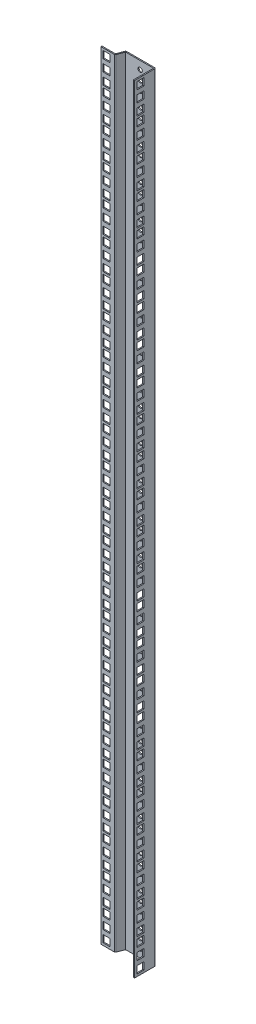
SolidWorks part; units mm, degrees
material "AISI 1020 钢，冷轧"
ref_plane "前视基准面" through (0, 0, 0) normal (0, 0, 1) x (1, 0, 0)
ref_plane "上视基准面" through (0, 0, 0) normal (0, 1, 0) x (1, 0, 0)
ref_plane "右视基准面" through (0, 0, 0) normal (1, 0, 0) x (0, 0, -1)
sketch "草图1" plane through (0, 0, 0) normal (0, 1, 0) x (1, 0, 0)
  line L0 (-1.5473, -0.7176) -> (16.9527, -0.7176)
  line L2 (16.9527, 0.7824) -> (-1.5473, 0.7824)
  line L3 (-1.5473, 0.7824) -> (-1.5473, -0.7176)
  line L4 (21.9526, 9.7824) -> (18.356, 0.2527)
  line L6 (21.9526, 11.2824) -> (60.4526, 11.2824)
  line L8 (60.4526, 9.7824) -> (21.9526, 9.7824)
  line L9 (16.9527, 0.7824) -> (20.5492, 10.312)
  line L11 (61.9526, 9.7824) -> (61.9526, -17.7176)
  line L12 (60.4526, 9.7824) -> (60.4526, -17.7176)
  line L13 (60.4526, -17.7176) -> (61.9526, -17.7176)
  arc A0 (21.9526, 11.2824) -> (20.5492, 10.312) centre (21.9526, 9.7824) ccw
  arc A1 (18.356, 0.2527) -> (16.9527, -0.7176) centre (16.9527, 0.7824) cw
  arc A2 (60.4526, 11.2824) -> (61.9526, 9.7824) centre (60.4526, 9.7824) cw
extrude "凸台-拉伸1" add sketch "草图1" along normal blind 1070
sketch "草图2" plane through (0, 0, -9.7824) normal (0, 0, 1) x (1, 0, 0)
  line L0 (1.4527, 666.95) -> (1.4527, 657.0516)
  line L1 (1.4527, 1067) -> (1.4527, 1057.1016)
  line L3 (1.4527, 1022.55) -> (1.4527, 1012.6516)
  line L4 (1.4527, 622.5) -> (1.4527, 612.6016)
  line L5 (1.4527, 1067) -> (11.0527, 1067)
  line L6 (11.0527, 1067) -> (11.0527, 1057.1016)
  line L7 (11.0527, 1057.1016) -> (1.4527, 1057.1016)
  line L8 (1.4527, 1035.4484) -> (1.4527, 1025.55)
  line L9 (1.4527, 1035.4484) -> (11.0527, 1035.4484)
  line L10 (11.0527, 1035.4484) -> (11.0527, 1025.55)
  line L11 (11.0527, 1025.55) -> (1.4527, 1025.55)
  line L12 (1.4527, 1022.55) -> (11.0527, 1022.55)
  line L13 (11.0527, 1022.55) -> (11.0527, 1012.6516)
  line L14 (1.4527, 1051.2242) -> (1.4527, 1041.3258)
  line L15 (1.4527, 1051.2242) -> (11.0527, 1051.2242)
  line L16 (11.0527, 1051.2242) -> (11.0527, 1041.3258)
  line L17 (11.0527, 1041.3258) -> (1.4527, 1041.3258)
  line L18 (1.4527, 889.2) -> (1.4527, 879.3016)
  line L19 (11.0527, 1012.6516) -> (1.4527, 1012.6516)
  line L20 (1.4527, 990.9984) -> (1.4527, 981.1)
  line L21 (1.4527, 990.9984) -> (11.0527, 990.9984)
  line L22 (11.0527, 990.9984) -> (11.0527, 981.1)
  line L23 (11.0527, 981.1) -> (1.4527, 981.1)
  line L24 (1.4527, 1006.7742) -> (1.4527, 996.8758)
  line L25 (1.4527, 1006.7742) -> (11.0527, 1006.7742)
  line L26 (11.0527, 1006.7742) -> (11.0527, 996.8758)
  line L27 (11.0527, 996.8758) -> (1.4527, 996.8758)
  line L28 (1.4527, 666.95) -> (11.0527, 666.95)
  line L29 (1.4527, 978.1) -> (1.4527, 968.2016)
  line L30 (1.4527, 933.65) -> (1.4527, 923.7516)
  line L31 (1.4527, 978.1) -> (11.0527, 978.1)
  line L32 (11.0527, 978.1) -> (11.0527, 968.2016)
  line L33 (11.0527, 968.2016) -> (1.4527, 968.2016)
  line L34 (1.4527, 946.5484) -> (1.4527, 936.65)
  line L35 (1.4527, 946.5484) -> (11.0527, 946.5484)
  line L36 (11.0527, 946.5484) -> (11.0527, 936.65)
  line L37 (11.0527, 936.65) -> (1.4527, 936.65)
  line L38 (1.4527, 933.65) -> (11.0527, 933.65)
  line L39 (11.0527, 933.65) -> (11.0527, 923.7516)
  line L40 (1.4527, 962.3242) -> (1.4527, 952.4258)
  line L41 (1.4527, 962.3242) -> (11.0527, 962.3242)
  line L42 (11.0527, 962.3242) -> (11.0527, 952.4258)
  line L43 (11.0527, 952.4258) -> (1.4527, 952.4258)
  line L44 (11.0527, 923.7516) -> (1.4527, 923.7516)
  line L45 (1.4527, 902.0984) -> (1.4527, 892.2)
  line L46 (1.4527, 902.0984) -> (11.0527, 902.0984)
  line L47 (11.0527, 902.0984) -> (11.0527, 892.2)
  line L48 (11.0527, 892.2) -> (1.4527, 892.2)
  line L49 (1.4527, 917.8742) -> (1.4527, 907.9758)
  line L50 (1.4527, 917.8742) -> (11.0527, 917.8742)
  line L51 (11.0527, 917.8742) -> (11.0527, 907.9758)
  line L52 (11.0527, 907.9758) -> (1.4527, 907.9758)
  line L53 (1.4527, 844.75) -> (1.4527, 834.8516)
  line L54 (1.4527, 889.2) -> (11.0527, 889.2)
  line L55 (11.0527, 889.2) -> (11.0527, 879.3016)
  line L56 (11.0527, 879.3016) -> (1.4527, 879.3016)
  line L57 (1.4527, 857.6484) -> (1.4527, 847.75)
  line L58 (1.4527, 857.6484) -> (11.0527, 857.6484)
  line L59 (11.0527, 857.6484) -> (11.0527, 847.75)
  line L60 (11.0527, 847.75) -> (1.4527, 847.75)
  line L61 (1.4527, 844.75) -> (11.0527, 844.75)
  line L62 (11.0527, 844.75) -> (11.0527, 834.8516)
  line L63 (1.4527, 873.4242) -> (1.4527, 863.5258)
  line L64 (1.4527, 873.4242) -> (11.0527, 873.4242)
  line L65 (11.0527, 873.4242) -> (11.0527, 863.5258)
  line L66 (11.0527, 863.5258) -> (1.4527, 863.5258)
  line L67 (11.0527, 834.8516) -> (1.4527, 834.8516)
  line L68 (1.4527, 813.1984) -> (1.4527, 803.3)
  line L69 (1.4527, 813.1984) -> (11.0527, 813.1984)
  line L70 (11.0527, 813.1984) -> (11.0527, 803.3)
  line L71 (11.0527, 803.3) -> (1.4527, 803.3)
  line L72 (1.4527, 828.9742) -> (1.4527, 819.0758)
  line L73 (1.4527, 828.9742) -> (11.0527, 828.9742)
  line L74 (11.0527, 828.9742) -> (11.0527, 819.0758)
  line L75 (11.0527, 819.0758) -> (1.4527, 819.0758)
  line L76 (33.9626, 832.025) -> (33.9626, 816.025)
  line L77 (49.9426, 816.025) -> (49.9426, 832.025)
  line L91 (1.4527, 800.3) -> (1.4527, 790.4016)
  line L92 (1.4527, 800.3) -> (11.0527, 800.3)
  line L93 (11.0527, 800.3) -> (11.0527, 790.4016)
  line L94 (11.0527, 790.4016) -> (1.4527, 790.4016)
  line L95 (1.4527, 768.7484) -> (1.4527, 758.85)
  line L96 (1.4527, 768.7484) -> (11.0527, 768.7484)
  line L97 (11.0527, 768.7484) -> (11.0527, 758.85)
  line L98 (11.0527, 758.85) -> (1.4527, 758.85)
  line L99 (1.4527, 784.5242) -> (1.4527, 774.6258)
  line L100 (1.4527, 784.5242) -> (11.0527, 784.5242)
  line L101 (11.0527, 784.5242) -> (11.0527, 774.6258)
  line L102 (11.0527, 774.6258) -> (1.4527, 774.6258)
  line L103 (33.9626, 787.575) -> (33.9626, 771.575)
  line L104 (49.9426, 771.575) -> (49.9426, 787.575)
  line L106 (1.4527, 755.85) -> (1.4527, 745.9516)
  line L107 (1.4527, 755.85) -> (11.0527, 755.85)
  line L108 (11.0527, 755.85) -> (11.0527, 745.9516)
  line L109 (11.0527, 745.9516) -> (1.4527, 745.9516)
  line L110 (1.4527, 724.2984) -> (1.4527, 714.4)
  line L111 (1.4527, 724.2984) -> (11.0527, 724.2984)
  line L112 (11.0527, 724.2984) -> (11.0527, 714.4)
  line L113 (11.0527, 714.4) -> (1.4527, 714.4)
  line L114 (1.4527, 740.0742) -> (1.4527, 730.1758)
  line L115 (1.4527, 740.0742) -> (11.0527, 740.0742)
  line L116 (11.0527, 740.0742) -> (11.0527, 730.1758)
  line L117 (11.0527, 730.1758) -> (1.4527, 730.1758)
  line L118 (33.9626, 743.125) -> (33.9626, 727.125)
  line L119 (49.9426, 727.125) -> (49.9426, 743.125)
  line L120 (1.4527, 711.4) -> (1.4527, 701.5016)
  line L121 (1.4527, 711.4) -> (11.0527, 711.4)
  line L122 (11.0527, 711.4) -> (11.0527, 701.5016)
  line L123 (11.0527, 701.5016) -> (1.4527, 701.5016)
  line L124 (1.4527, 679.8484) -> (1.4527, 669.95)
  line L125 (1.4527, 679.8484) -> (11.0527, 679.8484)
  line L126 (11.0527, 679.8484) -> (11.0527, 669.95)
  line L127 (11.0527, 669.95) -> (1.4527, 669.95)
  line L128 (1.4527, 695.6242) -> (1.4527, 685.7258)
  line L129 (1.4527, 695.6242) -> (11.0527, 695.6242)
  line L130 (11.0527, 695.6242) -> (11.0527, 685.7258)
  line L131 (11.0527, 685.7258) -> (1.4527, 685.7258)
  line L132 (33.9626, 698.675) -> (33.9626, 682.675)
  line L133 (49.9426, 682.675) -> (49.9426, 698.675)
  line L134 (11.0527, 666.95) -> (11.0527, 657.0516)
  line L135 (11.0527, 657.0516) -> (1.4527, 657.0516)
  line L136 (1.4527, 635.3984) -> (1.4527, 625.5)
  line L137 (1.4527, 635.3984) -> (11.0527, 635.3984)
  line L138 (11.0527, 635.3984) -> (11.0527, 625.5)
  line L139 (11.0527, 625.5) -> (1.4527, 625.5)
  line L140 (1.4527, 622.5) -> (11.0527, 622.5)
  line L141 (11.0527, 622.5) -> (11.0527, 612.6016)
  line L142 (1.4527, 651.1742) -> (1.4527, 641.2758)
  line L143 (1.4527, 651.1742) -> (11.0527, 651.1742)
  line L144 (11.0527, 651.1742) -> (11.0527, 641.2758)
  line L145 (11.0527, 641.2758) -> (1.4527, 641.2758)
  line L146 (1.4527, 489.15) -> (1.4527, 479.2516)
  line L147 (11.0527, 612.6016) -> (1.4527, 612.6016)
  line L148 (1.4527, 590.9484) -> (1.4527, 581.05)
  line L149 (1.4527, 590.9484) -> (11.0527, 590.9484)
  line L150 (11.0527, 590.9484) -> (11.0527, 581.05)
  line L151 (11.0527, 581.05) -> (1.4527, 581.05)
  line L152 (1.4527, 606.7242) -> (1.4527, 596.8258)
  line L153 (1.4527, 606.7242) -> (11.0527, 606.7242)
  line L154 (11.0527, 606.7242) -> (11.0527, 596.8258)
  line L155 (11.0527, 596.8258) -> (1.4527, 596.8258)
  line L156 (1.4527, 578.05) -> (1.4527, 568.1516)
  line L157 (1.4527, 533.6) -> (1.4527, 523.7016)
  line L158 (1.4527, 578.05) -> (11.0527, 578.05)
  line L159 (11.0527, 578.05) -> (11.0527, 568.1516)
  line L160 (11.0527, 568.1516) -> (1.4527, 568.1516)
  line L161 (1.4527, 546.4984) -> (1.4527, 536.6)
  line L162 (1.4527, 546.4984) -> (11.0527, 546.4984)
  line L163 (11.0527, 546.4984) -> (11.0527, 536.6)
  line L164 (11.0527, 536.6) -> (1.4527, 536.6)
  line L165 (1.4527, 533.6) -> (11.0527, 533.6)
  line L166 (11.0527, 533.6) -> (11.0527, 523.7016)
  line L167 (1.4527, 562.2742) -> (1.4527, 552.3758)
  line L168 (1.4527, 562.2742) -> (11.0527, 562.2742)
  line L169 (11.0527, 562.2742) -> (11.0527, 552.3758)
  line L170 (11.0527, 552.3758) -> (1.4527, 552.3758)
  line L171 (11.0527, 523.7016) -> (1.4527, 523.7016)
  line L172 (1.4527, 502.0484) -> (1.4527, 492.15)
  line L173 (1.4527, 502.0484) -> (11.0527, 502.0484)
  line L174 (11.0527, 502.0484) -> (11.0527, 492.15)
  line L175 (11.0527, 492.15) -> (1.4527, 492.15)
  line L176 (1.4527, 517.8242) -> (1.4527, 507.9258)
  line L177 (1.4527, 517.8242) -> (11.0527, 517.8242)
  line L178 (11.0527, 517.8242) -> (11.0527, 507.9258)
  line L179 (11.0527, 507.9258) -> (1.4527, 507.9258)
  line L180 (1.4527, 444.7) -> (1.4527, 434.8016)
  line L181 (1.4527, 489.15) -> (11.0527, 489.15)
  line L182 (11.0527, 489.15) -> (11.0527, 479.2516)
  line L183 (11.0527, 479.2516) -> (1.4527, 479.2516)
  line L184 (1.4527, 457.5984) -> (1.4527, 447.7)
  line L185 (1.4527, 457.5984) -> (11.0527, 457.5984)
  line L186 (11.0527, 457.5984) -> (11.0527, 447.7)
  line L187 (11.0527, 447.7) -> (1.4527, 447.7)
  line L188 (1.4527, 444.7) -> (11.0527, 444.7)
  line L189 (11.0527, 444.7) -> (11.0527, 434.8016)
  line L190 (1.4527, 473.3742) -> (1.4527, 463.4758)
  line L191 (1.4527, 473.3742) -> (11.0527, 473.3742)
  line L192 (11.0527, 473.3742) -> (11.0527, 463.4758)
  line L193 (11.0527, 463.4758) -> (1.4527, 463.4758)
  line L194 (11.0527, 434.8016) -> (1.4527, 434.8016)
  line L195 (1.4527, 413.1484) -> (1.4527, 403.25)
  line L196 (1.4527, 413.1484) -> (11.0527, 413.1484)
  line L197 (11.0527, 413.1484) -> (11.0527, 403.25)
  line L198 (11.0527, 403.25) -> (1.4527, 403.25)
  line L199 (1.4527, 428.9242) -> (1.4527, 419.0258)
  line L200 (1.4527, 428.9242) -> (11.0527, 428.9242)
  line L201 (11.0527, 428.9242) -> (11.0527, 419.0258)
  line L202 (11.0527, 419.0258) -> (1.4527, 419.0258)
  line L203 (33.9626, 431.975) -> (33.9626, 415.975)
  line L204 (49.9426, 415.975) -> (49.9426, 431.975)
  line L205 (1.4527, 400.25) -> (1.4527, 390.3516)
  line L206 (1.4527, 400.25) -> (11.0527, 400.25)
  line L207 (11.0527, 400.25) -> (11.0527, 390.3516)
  line L208 (11.0527, 390.3516) -> (1.4527, 390.3516)
  line L209 (1.4527, 368.6984) -> (1.4527, 358.8)
  line L210 (1.4527, 368.6984) -> (11.0527, 368.6984)
  line L211 (11.0527, 368.6984) -> (11.0527, 358.8)
  line L212 (11.0527, 358.8) -> (1.4527, 358.8)
  line L213 (1.4527, 384.4742) -> (1.4527, 374.5758)
  line L214 (1.4527, 384.4742) -> (11.0527, 384.4742)
  line L215 (11.0527, 384.4742) -> (11.0527, 374.5758)
  line L216 (11.0527, 374.5758) -> (1.4527, 374.5758)
  line L217 (33.9626, 387.525) -> (33.9626, 371.525)
  line L218 (49.9426, 371.525) -> (49.9426, 387.525)
  line L220 (1.4527, 355.8) -> (1.4527, 345.9016)
  line L221 (1.4527, 355.8) -> (11.0527, 355.8)
  line L222 (11.0527, 355.8) -> (11.0527, 345.9016)
  line L223 (11.0527, 345.9016) -> (1.4527, 345.9016)
  line L224 (1.4527, 324.2484) -> (1.4527, 314.35)
  line L225 (1.4527, 324.2484) -> (11.0527, 324.2484)
  line L226 (11.0527, 324.2484) -> (11.0527, 314.35)
  line L227 (11.0527, 314.35) -> (1.4527, 314.35)
  line L228 (1.4527, 340.0242) -> (1.4527, 330.1258)
  line L229 (1.4527, 340.0242) -> (11.0527, 340.0242)
  line L230 (11.0527, 340.0242) -> (11.0527, 330.1258)
  line L231 (11.0527, 330.1258) -> (1.4527, 330.1258)
  line L232 (33.9626, 343.075) -> (33.9626, 327.075)
  line L233 (49.9426, 327.075) -> (49.9426, 343.075)
  line L234 (1.4527, 311.35) -> (1.4527, 301.4516)
  line L235 (1.4527, 311.35) -> (11.0527, 311.35)
  line L236 (11.0527, 311.35) -> (11.0527, 301.4516)
  line L237 (11.0527, 301.4516) -> (1.4527, 301.4516)
  line L238 (1.4527, 279.7984) -> (1.4527, 269.9)
  line L239 (1.4527, 279.7984) -> (11.0527, 279.7984)
  line L240 (11.0527, 279.7984) -> (11.0527, 269.9)
  line L241 (11.0527, 269.9) -> (1.4527, 269.9)
  line L242 (1.4527, 295.5742) -> (1.4527, 285.6758)
  line L243 (1.4527, 295.5742) -> (11.0527, 295.5742)
  line L244 (11.0527, 295.5742) -> (11.0527, 285.6758)
  line L245 (11.0527, 285.6758) -> (1.4527, 285.6758)
  line L246 (33.9626, 298.625) -> (33.9626, 282.625)
  line L247 (49.9426, 282.625) -> (49.9426, 298.625)
  line L248 (1.4527, 266.9) -> (1.4527, 257.0016)
  line L249 (1.4527, 222.45) -> (1.4527, 212.5516)
  line L250 (1.4527, 266.9) -> (11.0527, 266.9)
  line L251 (11.0527, 266.9) -> (11.0527, 257.0016)
  line L252 (11.0527, 257.0016) -> (1.4527, 257.0016)
  line L253 (1.4527, 235.3484) -> (1.4527, 225.45)
  line L254 (1.4527, 235.3484) -> (11.0527, 235.3484)
  line L255 (11.0527, 235.3484) -> (11.0527, 225.45)
  line L256 (11.0527, 225.45) -> (1.4527, 225.45)
  line L257 (1.4527, 222.45) -> (11.0527, 222.45)
  line L258 (11.0527, 222.45) -> (11.0527, 212.5516)
  line L259 (1.4527, 251.1242) -> (1.4527, 241.2258)
  line L260 (1.4527, 251.1242) -> (11.0527, 251.1242)
  line L261 (11.0527, 251.1242) -> (11.0527, 241.2258)
  line L262 (11.0527, 241.2258) -> (1.4527, 241.2258)
  line L263 (1.4527, 89.1) -> (1.4527, 79.2016)
  line L264 (11.0527, 212.5516) -> (1.4527, 212.5516)
  line L265 (1.4527, 190.8984) -> (1.4527, 181)
  line L266 (1.4527, 190.8984) -> (11.0527, 190.8984)
  line L267 (11.0527, 190.8984) -> (11.0527, 181)
  line L268 (11.0527, 181) -> (1.4527, 181)
  line L269 (1.4527, 206.6742) -> (1.4527, 196.7758)
  line L270 (1.4527, 206.6742) -> (11.0527, 206.6742)
  line L271 (11.0527, 206.6742) -> (11.0527, 196.7758)
  line L272 (11.0527, 196.7758) -> (1.4527, 196.7758)
  line L273 (1.4527, 178) -> (1.4527, 168.1016)
  line L274 (1.4527, 133.55) -> (1.4527, 123.6516)
  line L275 (1.4527, 178) -> (11.0527, 178)
  line L276 (11.0527, 178) -> (11.0527, 168.1016)
  line L277 (11.0527, 168.1016) -> (1.4527, 168.1016)
  line L278 (1.4527, 146.4484) -> (1.4527, 136.55)
  line L279 (1.4527, 146.4484) -> (11.0527, 146.4484)
  line L280 (11.0527, 146.4484) -> (11.0527, 136.55)
  line L281 (11.0527, 136.55) -> (1.4527, 136.55)
  line L282 (1.4527, 133.55) -> (11.0527, 133.55)
  line L283 (11.0527, 133.55) -> (11.0527, 123.6516)
  line L284 (1.4527, 162.2242) -> (1.4527, 152.3258)
  line L285 (1.4527, 162.2242) -> (11.0527, 162.2242)
  line L286 (11.0527, 162.2242) -> (11.0527, 152.3258)
  line L287 (11.0527, 152.3258) -> (1.4527, 152.3258)
  line L288 (11.0527, 123.6516) -> (1.4527, 123.6516)
  line L289 (1.4527, 101.9984) -> (1.4527, 92.1)
  line L290 (1.4527, 101.9984) -> (11.0527, 101.9984)
  line L291 (11.0527, 101.9984) -> (11.0527, 92.1)
  line L292 (11.0527, 92.1) -> (1.4527, 92.1)
  line L293 (1.4527, 117.7742) -> (1.4527, 107.8758)
  line L294 (1.4527, 117.7742) -> (11.0527, 117.7742)
  line L295 (11.0527, 117.7742) -> (11.0527, 107.8758)
  line L296 (11.0527, 107.8758) -> (1.4527, 107.8758)
  line L297 (1.4527, 44.65) -> (1.4527, 34.7516)
  line L298 (1.4527, 89.1) -> (11.0527, 89.1)
  line L299 (11.0527, 89.1) -> (11.0527, 79.2016)
  line L300 (11.0527, 79.2016) -> (1.4527, 79.2016)
  line L301 (1.4527, 57.5484) -> (1.4527, 47.65)
  line L302 (1.4527, 57.5484) -> (11.0527, 57.5484)
  line L303 (11.0527, 57.5484) -> (11.0527, 47.65)
  line L304 (11.0527, 47.65) -> (1.4527, 47.65)
  line L305 (1.4527, 44.65) -> (11.0527, 44.65)
  line L306 (11.0527, 44.65) -> (11.0527, 34.7516)
  line L307 (1.4527, 73.3242) -> (1.4527, 63.4258)
  line L308 (1.4527, 73.3242) -> (11.0527, 73.3242)
  line L309 (11.0527, 73.3242) -> (11.0527, 63.4258)
  line L310 (11.0527, 63.4258) -> (1.4527, 63.4258)
  line L311 (11.0527, 34.7516) -> (1.4527, 34.7516)
  line L312 (1.4527, 13.0984) -> (1.4527, 3.2)
  line L313 (1.4527, 13.0984) -> (11.0527, 13.0984)
  line L314 (11.0527, 13.0984) -> (11.0527, 3.2)
  line L315 (11.0527, 3.2) -> (1.4527, 3.2)
  line L316 (1.4527, 28.8742) -> (1.4527, 18.9758)
  line L317 (1.4527, 28.8742) -> (11.0527, 28.8742)
  line L318 (11.0527, 28.8742) -> (11.0527, 18.9758)
  line L319 (11.0527, 18.9758) -> (1.4527, 18.9758)
  circle A0 centre (41.9526, 1046.275) radius 3
  circle A1 centre (41.9526, 1058.775) radius 3
  circle A2 centre (41.9526, 1033.775) radius 3
  circle A3 centre (41.9526, 1001.825) radius 3
  circle A4 centre (41.9526, 1014.325) radius 3
  circle A5 centre (41.9526, 989.325) radius 3
  circle A6 centre (41.9526, 957.375) radius 3
  circle A7 centre (41.9526, 969.875) radius 3
  circle A8 centre (41.9526, 944.875) radius 3
  circle A9 centre (41.9526, 912.925) radius 3
  circle A10 centre (41.9526, 925.425) radius 3
  circle A11 centre (41.9526, 900.425) radius 3
  circle A12 centre (41.9526, 868.475) radius 3
  circle A13 centre (41.9526, 880.975) radius 3
  circle A14 centre (41.9526, 855.975) radius 3
  arc A18 (49.9426, 832.025) -> (33.9626, 832.025) centre (41.9526, 832.025) ccw
  arc A19 (33.9626, 816.025) -> (49.9426, 816.025) centre (41.9526, 816.025) ccw
  arc A22 (49.9426, 787.575) -> (33.9626, 787.575) centre (41.9526, 787.575) ccw
  arc A23 (33.9626, 771.575) -> (49.9426, 771.575) centre (41.9526, 771.575) ccw
  arc A24 (49.9426, 743.125) -> (33.9626, 743.125) centre (41.9526, 743.125) ccw
  arc A25 (33.9626, 727.125) -> (49.9426, 727.125) centre (41.9526, 727.125) ccw
  arc A26 (49.9426, 698.675) -> (33.9626, 698.675) centre (41.9526, 698.675) ccw
  arc A27 (33.9626, 682.675) -> (49.9426, 682.675) centre (41.9526, 682.675) ccw
  circle A28 centre (41.9526, 646.225) radius 3
  circle A29 centre (41.9526, 658.725) radius 3
  circle A30 centre (41.9526, 633.725) radius 3
  circle A31 centre (41.9526, 601.775) radius 3
  circle A32 centre (41.9526, 614.275) radius 3
  circle A33 centre (41.9526, 589.275) radius 3
  circle A34 centre (41.9526, 557.325) radius 3
  circle A35 centre (41.9526, 569.825) radius 3
  circle A36 centre (41.9526, 544.825) radius 3
  circle A37 centre (41.9526, 512.875) radius 3
  circle A38 centre (41.9526, 525.375) radius 3
  circle A39 centre (41.9526, 500.375) radius 3
  circle A40 centre (41.9526, 468.425) radius 3
  circle A41 centre (41.9526, 480.925) radius 3
  circle A42 centre (41.9526, 455.925) radius 3
  arc A43 (49.9426, 431.975) -> (33.9626, 431.975) centre (41.9526, 431.975) ccw
  arc A44 (33.9626, 415.975) -> (49.9426, 415.975) centre (41.9526, 415.975) ccw
  arc A45 (49.9426, 387.525) -> (33.9626, 387.525) centre (41.9526, 387.525) ccw
  arc A46 (33.9626, 371.525) -> (49.9426, 371.525) centre (41.9526, 371.525) ccw
  arc A47 (49.9426, 343.075) -> (33.9626, 343.075) centre (41.9526, 343.075) ccw
  arc A48 (33.9626, 327.075) -> (49.9426, 327.075) centre (41.9526, 327.075) ccw
  arc A49 (49.9426, 298.625) -> (33.9626, 298.625) centre (41.9526, 298.625) ccw
  arc A50 (33.9626, 282.625) -> (49.9426, 282.625) centre (41.9526, 282.625) ccw
  circle A51 centre (41.9526, 246.175) radius 3
  circle A52 centre (41.9526, 258.675) radius 3
  circle A53 centre (41.9526, 233.675) radius 3
  circle A54 centre (41.9526, 201.725) radius 3
  circle A55 centre (41.9526, 214.225) radius 3
  circle A56 centre (41.9526, 189.225) radius 3
  circle A57 centre (41.9526, 157.275) radius 3
  circle A58 centre (41.9526, 169.775) radius 3
  circle A59 centre (41.9526, 144.775) radius 3
  circle A60 centre (41.9526, 112.825) radius 3
  circle A61 centre (41.9526, 125.325) radius 3
  circle A62 centre (41.9526, 100.325) radius 3
  circle A63 centre (41.9526, 68.375) radius 3
  circle A64 centre (41.9526, 80.875) radius 3
  circle A65 centre (41.9526, 55.875) radius 3
  circle A68 centre (41.9526, 23.925) radius 3
  circle A69 centre (41.9526, 36.425) radius 3
  circle A70 centre (41.9526, 11.425) radius 3
sketch "草图4" plane through (61.9526, 0, 0) normal (1, 0, 0) x (0, 0, -1)
  line L0 (-14.7176, 666.95) -> (-14.7176, 657.0516)
  line L1 (-14.7176, 1067) -> (-14.7176, 1057.1016)
  line L2 (-14.7176, 1022.55) -> (-14.7176, 1012.6516)
  line L3 (-14.7176, 622.5) -> (-14.7176, 612.6016)
  line L4 (-14.7176, 1067) -> (-5.1176, 1067)
  line L5 (-5.1176, 1067) -> (-5.1176, 1057.1016)
  line L6 (-5.1176, 1057.1016) -> (-14.7176, 1057.1016)
  line L7 (-14.7176, 1035.4484) -> (-14.7176, 1025.55)
  line L8 (-14.7176, 1035.4484) -> (-5.1176, 1035.4484)
  line L9 (-5.1176, 1035.4484) -> (-5.1176, 1025.55)
  line L10 (-5.1176, 1025.55) -> (-14.7176, 1025.55)
  line L11 (-14.7176, 1022.55) -> (-5.1176, 1022.55)
  line L12 (-5.1176, 1022.55) -> (-5.1176, 1012.6516)
  line L13 (-14.7176, 1051.2242) -> (-14.7176, 1041.3258)
  line L14 (-14.7176, 1051.2242) -> (-5.1176, 1051.2242)
  line L15 (-5.1176, 1051.2242) -> (-5.1176, 1041.3258)
  line L16 (-5.1176, 1041.3258) -> (-14.7176, 1041.3258)
  line L17 (-14.7176, 889.2) -> (-14.7176, 879.3016)
  line L18 (-5.1176, 1012.6516) -> (-14.7176, 1012.6516)
  line L19 (-14.7176, 990.9984) -> (-14.7176, 981.1)
  line L20 (-14.7176, 990.9984) -> (-5.1176, 990.9984)
  line L21 (-5.1176, 990.9984) -> (-5.1176, 981.1)
  line L22 (-5.1176, 981.1) -> (-14.7176, 981.1)
  line L23 (-14.7176, 1006.7742) -> (-14.7176, 996.8758)
  line L24 (-14.7176, 1006.7742) -> (-5.1176, 1006.7742)
  line L25 (-5.1176, 1006.7742) -> (-5.1176, 996.8758)
  line L26 (-5.1176, 996.8758) -> (-14.7176, 996.8758)
  line L27 (-14.7176, 666.95) -> (-5.1176, 666.95)
  line L28 (-14.7176, 978.1) -> (-14.7176, 968.2016)
  line L29 (-14.7176, 933.65) -> (-14.7176, 923.7516)
  line L30 (-14.7176, 978.1) -> (-5.1176, 978.1)
  line L31 (-5.1176, 978.1) -> (-5.1176, 968.2016)
  line L32 (-5.1176, 968.2016) -> (-14.7176, 968.2016)
  line L33 (-14.7176, 946.5484) -> (-14.7176, 936.65)
  line L34 (-14.7176, 946.5484) -> (-5.1176, 946.5484)
  line L35 (-5.1176, 946.5484) -> (-5.1176, 936.65)
  line L36 (-5.1176, 936.65) -> (-14.7176, 936.65)
  line L37 (-14.7176, 933.65) -> (-5.1176, 933.65)
  line L38 (-5.1176, 933.65) -> (-5.1176, 923.7516)
  line L39 (-14.7176, 962.3242) -> (-14.7176, 952.4258)
  line L40 (-14.7176, 962.3242) -> (-5.1176, 962.3242)
  line L41 (-5.1176, 962.3242) -> (-5.1176, 952.4258)
  line L42 (-5.1176, 952.4258) -> (-14.7176, 952.4258)
  line L43 (-5.1176, 923.7516) -> (-14.7176, 923.7516)
  line L44 (-14.7176, 902.0984) -> (-14.7176, 892.2)
  line L45 (-14.7176, 902.0984) -> (-5.1176, 902.0984)
  line L46 (-5.1176, 902.0984) -> (-5.1176, 892.2)
  line L47 (-5.1176, 892.2) -> (-14.7176, 892.2)
  line L48 (-14.7176, 917.8742) -> (-14.7176, 907.9758)
  line L49 (-14.7176, 917.8742) -> (-5.1176, 917.8742)
  line L50 (-5.1176, 917.8742) -> (-5.1176, 907.9758)
  line L51 (-5.1176, 907.9758) -> (-14.7176, 907.9758)
  line L52 (-14.7176, 844.75) -> (-14.7176, 834.8516)
  line L53 (-14.7176, 889.2) -> (-5.1176, 889.2)
  line L54 (-5.1176, 889.2) -> (-5.1176, 879.3016)
  line L55 (-5.1176, 879.3016) -> (-14.7176, 879.3016)
  line L56 (-14.7176, 857.6484) -> (-14.7176, 847.75)
  line L57 (-14.7176, 857.6484) -> (-5.1176, 857.6484)
  line L58 (-5.1176, 857.6484) -> (-5.1176, 847.75)
  line L59 (-5.1176, 847.75) -> (-14.7176, 847.75)
  line L60 (-14.7176, 844.75) -> (-5.1176, 844.75)
  line L61 (-5.1176, 844.75) -> (-5.1176, 834.8516)
  line L62 (-14.7176, 873.4242) -> (-14.7176, 863.5258)
  line L63 (-14.7176, 873.4242) -> (-5.1176, 873.4242)
  line L64 (-5.1176, 873.4242) -> (-5.1176, 863.5258)
  line L65 (-5.1176, 863.5258) -> (-14.7176, 863.5258)
  line L66 (-5.1176, 834.8516) -> (-14.7176, 834.8516)
  line L67 (-14.7176, 813.1984) -> (-14.7176, 803.3)
  line L68 (-14.7176, 813.1984) -> (-5.1176, 813.1984)
  line L69 (-5.1176, 813.1984) -> (-5.1176, 803.3)
  line L70 (-5.1176, 803.3) -> (-14.7176, 803.3)
  line L71 (-14.7176, 828.9742) -> (-14.7176, 819.0758)
  line L72 (-14.7176, 828.9742) -> (-5.1176, 828.9742)
  line L73 (-5.1176, 828.9742) -> (-5.1176, 819.0758)
  line L74 (-5.1176, 819.0758) -> (-14.7176, 819.0758)
  line L75 (-14.7176, 800.3) -> (-14.7176, 790.4016)
  line L76 (-14.7176, 800.3) -> (-5.1176, 800.3)
  line L77 (-5.1176, 800.3) -> (-5.1176, 790.4016)
  line L78 (-5.1176, 790.4016) -> (-14.7176, 790.4016)
  line L79 (-14.7176, 768.7484) -> (-14.7176, 758.85)
  line L80 (-14.7176, 768.7484) -> (-5.1176, 768.7484)
  line L81 (-5.1176, 768.7484) -> (-5.1176, 758.85)
  line L82 (-5.1176, 758.85) -> (-14.7176, 758.85)
  line L83 (-14.7176, 784.5242) -> (-14.7176, 774.6258)
  line L84 (-14.7176, 784.5242) -> (-5.1176, 784.5242)
  line L85 (-5.1176, 784.5242) -> (-5.1176, 774.6258)
  line L86 (-5.1176, 774.6258) -> (-14.7176, 774.6258)
  line L88 (-14.7176, 755.85) -> (-14.7176, 745.9516)
  line L89 (-14.7176, 755.85) -> (-5.1176, 755.85)
  line L90 (-5.1176, 755.85) -> (-5.1176, 745.9516)
  line L91 (-5.1176, 745.9516) -> (-14.7176, 745.9516)
  line L92 (-14.7176, 724.2984) -> (-14.7176, 714.4)
  line L93 (-14.7176, 724.2984) -> (-5.1176, 724.2984)
  line L94 (-5.1176, 724.2984) -> (-5.1176, 714.4)
  line L95 (-5.1176, 714.4) -> (-14.7176, 714.4)
  line L96 (-14.7176, 740.0742) -> (-14.7176, 730.1758)
  line L97 (-14.7176, 740.0742) -> (-5.1176, 740.0742)
  line L98 (-5.1176, 740.0742) -> (-5.1176, 730.1758)
  line L99 (-5.1176, 730.1758) -> (-14.7176, 730.1758)
  line L100 (-14.7176, 711.4) -> (-14.7176, 701.5016)
  line L101 (-14.7176, 711.4) -> (-5.1176, 711.4)
  line L102 (-5.1176, 711.4) -> (-5.1176, 701.5016)
  line L103 (-5.1176, 701.5016) -> (-14.7176, 701.5016)
  line L104 (-14.7176, 679.8484) -> (-14.7176, 669.95)
  line L105 (-14.7176, 679.8484) -> (-5.1176, 679.8484)
  line L106 (-5.1176, 679.8484) -> (-5.1176, 669.95)
  line L107 (-5.1176, 669.95) -> (-14.7176, 669.95)
  line L108 (-14.7176, 695.6242) -> (-14.7176, 685.7258)
  line L109 (-14.7176, 695.6242) -> (-5.1176, 695.6242)
  line L110 (-5.1176, 695.6242) -> (-5.1176, 685.7258)
  line L111 (-5.1176, 685.7258) -> (-14.7176, 685.7258)
  line L112 (-5.1176, 666.95) -> (-5.1176, 657.0516)
  line L113 (-5.1176, 657.0516) -> (-14.7176, 657.0516)
  line L114 (-14.7176, 635.3984) -> (-14.7176, 625.5)
  line L115 (-14.7176, 635.3984) -> (-5.1176, 635.3984)
  line L116 (-5.1176, 635.3984) -> (-5.1176, 625.5)
  line L117 (-5.1176, 625.5) -> (-14.7176, 625.5)
  line L118 (-14.7176, 622.5) -> (-5.1176, 622.5)
  line L119 (-5.1176, 622.5) -> (-5.1176, 612.6016)
  line L120 (-14.7176, 651.1742) -> (-14.7176, 641.2758)
  line L121 (-14.7176, 651.1742) -> (-5.1176, 651.1742)
  line L122 (-5.1176, 651.1742) -> (-5.1176, 641.2758)
  line L123 (-5.1176, 641.2758) -> (-14.7176, 641.2758)
  line L124 (-14.7176, 489.15) -> (-14.7176, 479.2516)
  line L125 (-5.1176, 612.6016) -> (-14.7176, 612.6016)
  line L126 (-14.7176, 590.9484) -> (-14.7176, 581.05)
  line L127 (-14.7176, 590.9484) -> (-5.1176, 590.9484)
  line L128 (-5.1176, 590.9484) -> (-5.1176, 581.05)
  line L129 (-5.1176, 581.05) -> (-14.7176, 581.05)
  line L130 (-14.7176, 606.7242) -> (-14.7176, 596.8258)
  line L131 (-14.7176, 606.7242) -> (-5.1176, 606.7242)
  line L132 (-5.1176, 606.7242) -> (-5.1176, 596.8258)
  line L133 (-5.1176, 596.8258) -> (-14.7176, 596.8258)
  line L134 (-14.7176, 578.05) -> (-14.7176, 568.1516)
  line L135 (-14.7176, 533.6) -> (-14.7176, 523.7016)
  line L136 (-14.7176, 578.05) -> (-5.1176, 578.05)
  line L137 (-5.1176, 578.05) -> (-5.1176, 568.1516)
  line L138 (-5.1176, 568.1516) -> (-14.7176, 568.1516)
  line L139 (-14.7176, 546.4984) -> (-14.7176, 536.6)
  line L140 (-14.7176, 546.4984) -> (-5.1176, 546.4984)
  line L141 (-5.1176, 546.4984) -> (-5.1176, 536.6)
  line L142 (-5.1176, 536.6) -> (-14.7176, 536.6)
  line L143 (-14.7176, 533.6) -> (-5.1176, 533.6)
  line L144 (-5.1176, 533.6) -> (-5.1176, 523.7016)
  line L145 (-14.7176, 562.2742) -> (-14.7176, 552.3758)
  line L146 (-14.7176, 562.2742) -> (-5.1176, 562.2742)
  line L147 (-5.1176, 562.2742) -> (-5.1176, 552.3758)
  line L148 (-5.1176, 552.3758) -> (-14.7176, 552.3758)
  line L149 (-5.1176, 523.7016) -> (-14.7176, 523.7016)
  line L150 (-14.7176, 502.0484) -> (-14.7176, 492.15)
  line L151 (-14.7176, 502.0484) -> (-5.1176, 502.0484)
  line L152 (-5.1176, 502.0484) -> (-5.1176, 492.15)
  line L153 (-5.1176, 492.15) -> (-14.7176, 492.15)
  line L154 (-14.7176, 517.8242) -> (-14.7176, 507.9258)
  line L155 (-14.7176, 517.8242) -> (-5.1176, 517.8242)
  line L156 (-5.1176, 517.8242) -> (-5.1176, 507.9258)
  line L157 (-5.1176, 507.9258) -> (-14.7176, 507.9258)
  line L158 (-14.7176, 444.7) -> (-14.7176, 434.8016)
  line L159 (-14.7176, 489.15) -> (-5.1176, 489.15)
  line L160 (-5.1176, 489.15) -> (-5.1176, 479.2516)
  line L161 (-5.1176, 479.2516) -> (-14.7176, 479.2516)
  line L162 (-14.7176, 457.5984) -> (-14.7176, 447.7)
  line L163 (-14.7176, 457.5984) -> (-5.1176, 457.5984)
  line L164 (-5.1176, 457.5984) -> (-5.1176, 447.7)
  line L165 (-5.1176, 447.7) -> (-14.7176, 447.7)
  line L166 (-14.7176, 444.7) -> (-5.1176, 444.7)
  line L167 (-5.1176, 444.7) -> (-5.1176, 434.8016)
  line L168 (-14.7176, 473.3742) -> (-14.7176, 463.4758)
  line L169 (-14.7176, 473.3742) -> (-5.1176, 473.3742)
  line L170 (-5.1176, 473.3742) -> (-5.1176, 463.4758)
  line L171 (-5.1176, 463.4758) -> (-14.7176, 463.4758)
  line L172 (-5.1176, 434.8016) -> (-14.7176, 434.8016)
  line L173 (-14.7176, 413.1484) -> (-14.7176, 403.25)
  line L174 (-14.7176, 413.1484) -> (-5.1176, 413.1484)
  line L175 (-5.1176, 413.1484) -> (-5.1176, 403.25)
  line L176 (-5.1176, 403.25) -> (-14.7176, 403.25)
  line L177 (-14.7176, 428.9242) -> (-14.7176, 419.0258)
  line L178 (-14.7176, 428.9242) -> (-5.1176, 428.9242)
  line L179 (-5.1176, 428.9242) -> (-5.1176, 419.0258)
  line L180 (-5.1176, 419.0258) -> (-14.7176, 419.0258)
  line L181 (-14.7176, 400.25) -> (-14.7176, 390.3516)
  line L182 (-14.7176, 400.25) -> (-5.1176, 400.25)
  line L183 (-5.1176, 400.25) -> (-5.1176, 390.3516)
  line L184 (-5.1176, 390.3516) -> (-14.7176, 390.3516)
  line L185 (-14.7176, 368.6984) -> (-14.7176, 358.8)
  line L186 (-14.7176, 368.6984) -> (-5.1176, 368.6984)
  line L187 (-5.1176, 368.6984) -> (-5.1176, 358.8)
  line L188 (-5.1176, 358.8) -> (-14.7176, 358.8)
  line L189 (-14.7176, 384.4742) -> (-14.7176, 374.5758)
  line L190 (-14.7176, 384.4742) -> (-5.1176, 384.4742)
  line L191 (-5.1176, 384.4742) -> (-5.1176, 374.5758)
  line L192 (-5.1176, 374.5758) -> (-14.7176, 374.5758)
  line L194 (-14.7176, 355.8) -> (-14.7176, 345.9016)
  line L195 (-14.7176, 355.8) -> (-5.1176, 355.8)
  line L196 (-5.1176, 355.8) -> (-5.1176, 345.9016)
  line L197 (-5.1176, 345.9016) -> (-14.7176, 345.9016)
  line L198 (-14.7176, 324.2484) -> (-14.7176, 314.35)
  line L199 (-14.7176, 324.2484) -> (-5.1176, 324.2484)
  line L200 (-5.1176, 324.2484) -> (-5.1176, 314.35)
  line L201 (-5.1176, 314.35) -> (-14.7176, 314.35)
  line L202 (-14.7176, 340.0242) -> (-14.7176, 330.1258)
  line L203 (-14.7176, 340.0242) -> (-5.1176, 340.0242)
  line L204 (-5.1176, 340.0242) -> (-5.1176, 330.1258)
  line L205 (-5.1176, 330.1258) -> (-14.7176, 330.1258)
  line L206 (-14.7176, 311.35) -> (-14.7176, 301.4516)
  line L207 (-14.7176, 311.35) -> (-5.1176, 311.35)
  line L208 (-5.1176, 311.35) -> (-5.1176, 301.4516)
  line L209 (-5.1176, 301.4516) -> (-14.7176, 301.4516)
  line L210 (-14.7176, 279.7984) -> (-14.7176, 269.9)
  line L211 (-14.7176, 279.7984) -> (-5.1176, 279.7984)
  line L212 (-5.1176, 279.7984) -> (-5.1176, 269.9)
  line L213 (-5.1176, 269.9) -> (-14.7176, 269.9)
  line L214 (-14.7176, 295.5742) -> (-14.7176, 285.6758)
  line L215 (-14.7176, 295.5742) -> (-5.1176, 295.5742)
  line L216 (-5.1176, 295.5742) -> (-5.1176, 285.6758)
  line L217 (-5.1176, 285.6758) -> (-14.7176, 285.6758)
  line L218 (-14.7176, 266.9) -> (-14.7176, 257.0016)
  line L219 (-14.7176, 222.45) -> (-14.7176, 212.5516)
  line L220 (-14.7176, 266.9) -> (-5.1176, 266.9)
  line L221 (-5.1176, 266.9) -> (-5.1176, 257.0016)
  line L222 (-5.1176, 257.0016) -> (-14.7176, 257.0016)
  line L223 (-14.7176, 235.3484) -> (-14.7176, 225.45)
  line L224 (-14.7176, 235.3484) -> (-5.1176, 235.3484)
  line L225 (-5.1176, 235.3484) -> (-5.1176, 225.45)
  line L226 (-5.1176, 225.45) -> (-14.7176, 225.45)
  line L227 (-14.7176, 222.45) -> (-5.1176, 222.45)
  line L228 (-5.1176, 222.45) -> (-5.1176, 212.5516)
  line L229 (-14.7176, 251.1242) -> (-14.7176, 241.2258)
  line L230 (-14.7176, 251.1242) -> (-5.1176, 251.1242)
  line L231 (-5.1176, 251.1242) -> (-5.1176, 241.2258)
  line L232 (-5.1176, 241.2258) -> (-14.7176, 241.2258)
  line L233 (-14.7176, 89.1) -> (-14.7176, 79.2016)
  line L234 (-5.1176, 212.5516) -> (-14.7176, 212.5516)
  line L235 (-14.7176, 190.8984) -> (-14.7176, 181)
  line L236 (-14.7176, 190.8984) -> (-5.1176, 190.8984)
  line L237 (-5.1176, 190.8984) -> (-5.1176, 181)
  line L238 (-5.1176, 181) -> (-14.7176, 181)
  line L239 (-14.7176, 206.6742) -> (-14.7176, 196.7758)
  line L240 (-14.7176, 206.6742) -> (-5.1176, 206.6742)
  line L241 (-5.1176, 206.6742) -> (-5.1176, 196.7758)
  line L242 (-5.1176, 196.7758) -> (-14.7176, 196.7758)
  line L243 (-14.7176, 178) -> (-14.7176, 168.1016)
  line L244 (-14.7176, 133.55) -> (-14.7176, 123.6516)
  line L245 (-14.7176, 178) -> (-5.1176, 178)
  line L246 (-5.1176, 178) -> (-5.1176, 168.1016)
  line L247 (-5.1176, 168.1016) -> (-14.7176, 168.1016)
  line L248 (-14.7176, 146.4484) -> (-14.7176, 136.55)
  line L249 (-14.7176, 146.4484) -> (-5.1176, 146.4484)
  line L250 (-5.1176, 146.4484) -> (-5.1176, 136.55)
  line L251 (-5.1176, 136.55) -> (-14.7176, 136.55)
  line L252 (-14.7176, 133.55) -> (-5.1176, 133.55)
  line L253 (-5.1176, 133.55) -> (-5.1176, 123.6516)
  line L254 (-14.7176, 162.2242) -> (-14.7176, 152.3258)
  line L255 (-14.7176, 162.2242) -> (-5.1176, 162.2242)
  line L256 (-5.1176, 162.2242) -> (-5.1176, 152.3258)
  line L257 (-5.1176, 152.3258) -> (-14.7176, 152.3258)
  line L258 (-5.1176, 123.6516) -> (-14.7176, 123.6516)
  line L259 (-14.7176, 101.9984) -> (-14.7176, 92.1)
  line L260 (-14.7176, 101.9984) -> (-5.1176, 101.9984)
  line L261 (-5.1176, 101.9984) -> (-5.1176, 92.1)
  line L262 (-5.1176, 92.1) -> (-14.7176, 92.1)
  line L263 (-14.7176, 117.7742) -> (-14.7176, 107.8758)
  line L264 (-14.7176, 117.7742) -> (-5.1176, 117.7742)
  line L265 (-5.1176, 117.7742) -> (-5.1176, 107.8758)
  line L266 (-5.1176, 107.8758) -> (-14.7176, 107.8758)
  line L267 (-14.7176, 44.65) -> (-14.7176, 34.7516)
  line L268 (-14.7176, 89.1) -> (-5.1176, 89.1)
  line L269 (-5.1176, 89.1) -> (-5.1176, 79.2016)
  line L270 (-5.1176, 79.2016) -> (-14.7176, 79.2016)
  line L271 (-14.7176, 57.5484) -> (-14.7176, 47.65)
  line L272 (-14.7176, 57.5484) -> (-5.1176, 57.5484)
  line L273 (-5.1176, 57.5484) -> (-5.1176, 47.65)
  line L274 (-5.1176, 47.65) -> (-14.7176, 47.65)
  line L275 (-14.7176, 44.65) -> (-5.1176, 44.65)
  line L276 (-5.1176, 44.65) -> (-5.1176, 34.7516)
  line L277 (-14.7176, 73.3242) -> (-14.7176, 63.4258)
  line L278 (-14.7176, 73.3242) -> (-5.1176, 73.3242)
  line L279 (-5.1176, 73.3242) -> (-5.1176, 63.4258)
  line L280 (-5.1176, 63.4258) -> (-14.7176, 63.4258)
  line L281 (-5.1176, 34.7516) -> (-14.7176, 34.7516)
  line L282 (-14.7176, 13.0984) -> (-14.7176, 3.2)
  line L283 (-14.7176, 13.0984) -> (-5.1176, 13.0984)
  line L284 (-5.1176, 13.0984) -> (-5.1176, 3.2)
  line L285 (-5.1176, 3.2) -> (-14.7176, 3.2)
  line L286 (-14.7176, 28.8742) -> (-14.7176, 18.9758)
  line L287 (-14.7176, 28.8742) -> (-5.1176, 28.8742)
  line L288 (-5.1176, 28.8742) -> (-5.1176, 18.9758)
  line L289 (-5.1176, 18.9758) -> (-14.7176, 18.9758)
extrude "切除-拉伸2" cut sketch "草图2" against normal blind 84 and the other way blind 39
extrude "切除-拉伸3" cut sketch "草图4" against normal blind 21 and the other way blind 26
